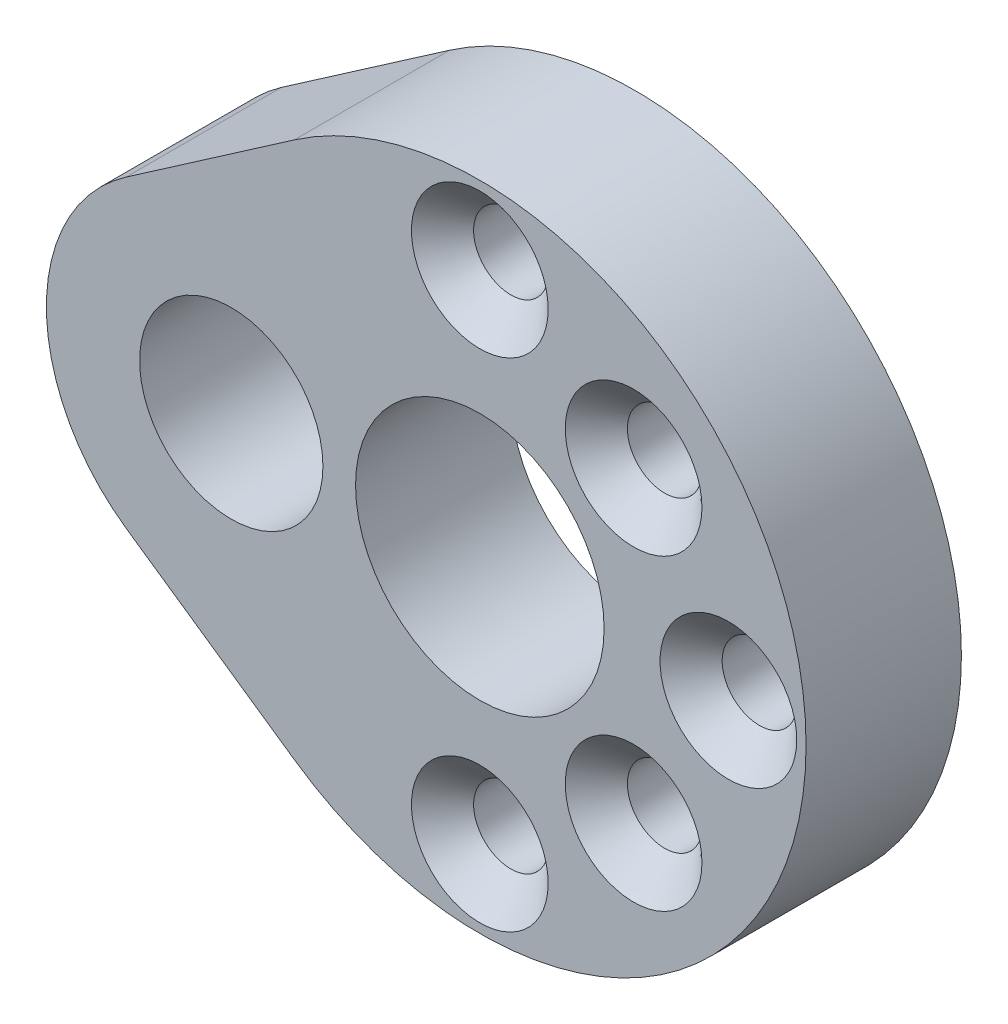
SolidWorks part; units mm, degrees
material "ABS"
ref_plane "Front Plane" through (0, 0, 0) normal (0, 0, 1) x (1, 0, 0)
ref_plane "Top Plane" through (0, 0, 0) normal (0, 1, 0) x (1, 0, 0)
ref_plane "Right Plane" through (0, 0, 0) normal (1, 0, 0) x (0, 0, -1)
sketch "Sketch1" plane through (0, 0, 0) normal (0, 0, 1) x (1, 0, 0)
  circle A0 centre (0, 0) radius 10.5
  circle A1 centre (-4.9497, 4.9497) radius 0.8
  circle A2 centre (0, 8) radius 0.8
  circle A3 centre (4.9497, 4.9497) radius 0.8
  circle A4 centre (8, 0) radius 0.8
  circle A5 centre (4.9497, -4.9497) radius 0.8
  circle A6 centre (0, -8) radius 0.8
  circle A7 centre (-4.9497, -4.9497) radius 0.8
  circle A8 centre (-8, 0) radius 0.8
  circle A9 centre (0, 0) radius 8 construction
  circle A10 centre (0, 0) radius 7 construction
  dimension "D1" = 21
  dimension "D2" = 1.6
  dimension "D3" = 16
  dimension "D4" = 14
extrude "Boss-Extrude1" add sketch "Sketch1" along normal blind 5
sketch "Sketch2" plane through (0, 0, 5) normal (0, 0, 1) x (1, 0, 0)
  circle A0 centre (-8, 0) radius 2.95
  circle A1 centre (-8, 0) radius 5.95
  dimension "D2" = 5.9
  dimension "D1" = 3
extrude "Boss-Extrude2" add sketch "Sketch2" against normal up to surface (5 mm away) up to face at (-4.1497, -4.9497, 0)
hole_wizard "CSK for M2 Countersunk Flat Head Screw1" positions "Sketch4" profile "Sketch3" countersink size "M2" standard "DIN" end condition through all
sketch "Sketch4" plane through (0, 0, 5) normal (0, 0, 1) x (1, 0, 0)
  point P0 (4.9497, 4.9497)
  point P1 (0, 8)
  point P4 (0, -8)
  point P7 (8, 0)
  point P16 (4.9497, -4.9497)
sketch "Sketch3" plane through (4.9497, 4.9497, 5) normal (1, 0, 0) x (0, -1, 0)
  line L0 (0, 0) -> (0, 5)
  line L1 (0, 5) -> (1.2, 5)
  line L2 (1.2, 5) -> (1.2, 1)
  line L3 (1.2, 1) -> (2.2, 0)
  line L5 (2.2, 0) -> (0, 0)
  line L6 (-1.2, 1) -> (-2.2, 0) construction
  line L11 (0, -6.35) -> (0, 107.95) construction
  dimension "Thru Hole Dia." = 2.4
  dimension "Thru Hole Depth" = 5
  dimension "Near C'Sink Dia." = 4.4
  dimension "Near C'Sink Angle" = 90
sketch "Sketch5" plane through (0, 0, 5) normal (0, 0, 1) x (1, 0, 0)
  circle A0 centre (-8, 0) radius 2.95
  arc A1 (-10.3467, 1.7876) -> (-10.3467, -1.7876) centre (-8, 0) ccw construction
extrude "Cut-Extrude1" cut sketch "Sketch5" against normal blind 5
sketch "Sketch6" plane through (0, 0, 5) normal (0, 0, 1) x (1, 0, 0)
  circle A0 centre (0, 0) radius 4
  dimension "D1" = 8
extrude "Cut-Extrude2" cut sketch "Sketch6" against normal blind 5
sketch "Sketch7" plane through (0, 0, 5) normal (0, 0, 1) x (1, 0, 0)
  line L0 (-11.3841, 4.8939) -> (-5.9719, 8.6364)
  line L1 (-11.3841, 4.8939) -> (-6.2331, 4.2024)
  line L2 (-6.2331, 4.2024) -> (-5.9719, 8.6364)
  arc A0 (-8.678, -5.9112) -> (-8.678, 5.9112) centre (0, 0) ccw construction
  arc A1 (-8.678, 5.9112) -> (-8.678, -5.9112) centre (-8, 0) ccw construction
extrude "Boss-Extrude3" add sketch "Sketch7" against normal up to surface (5 mm away) up to face at (4, 0, 0)
mirror "Mirror1" about plane through (0, 0, 0) normal (0, 1, 0) of "Boss-Extrude3"
sketch "Sketch8" plane through (0, 0, 5) normal (0, 0, 1) x (1, 0, 0)
  line L0 (0, 0) -> (-15.3567, 0) construction
  circle A0 centre (-4.9497, 4.9497) radius 0.8
  arc A1 (-4.2291, 4.6024) -> (-5.5839, 5.4374) centre (-4.9497, 4.9497) ccw construction
  circle A2 centre (-4.9497, -4.9497) radius 0.8
extrude "Boss-Extrude4" add sketch "Sketch8" against normal up to surface (5 mm away) up to face at (-5.2015, 0, 0)
